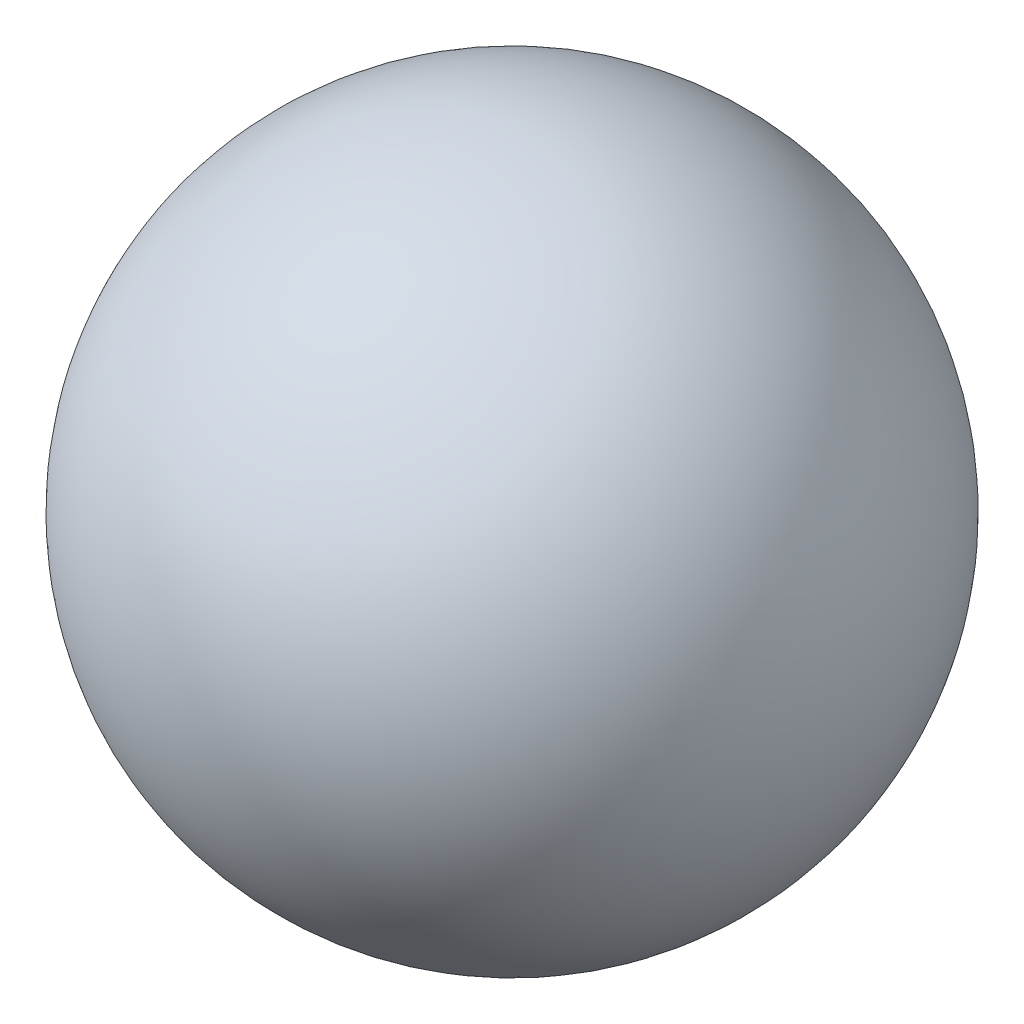
SolidWorks part; units mm, degrees
ref_plane "Alzado" through (0, 0, 0) normal (0, 0, 1) x (1, 0, 0)
ref_plane "Planta" through (0, 0, 0) normal (0, 1, 0) x (1, 0, 0)
ref_plane "Vista lateral" through (0, 0, 0) normal (1, 0, 0) x (0, 0, -1)
ref_plane "Plano1" through (0, 0, 0) normal (0, 0, 1) x (1, 0, 0)
sketch "Croquis1" plane through (0, 0, 0) normal (0, 0, 1) x (1, 0, 0)
  line L0 (10.572, 30) -> (3.428, 30)
  line L1 (50, 30) -> (-50, 30) construction
  arc A0 (3.428, 30) -> (10.572, 30) centre (7, 30) cw
revolve "Revolución1" add sketch "Croquis1" angle 360 about L1
